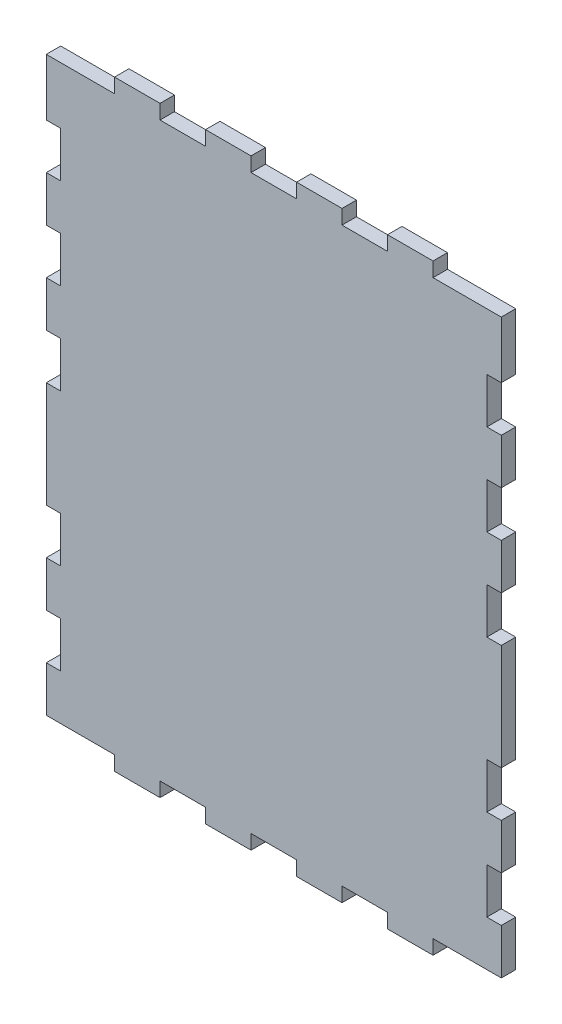
SolidWorks part; units mm, degrees
ref_plane "Front Plane" through (0, 0, 0) normal (0, 0, 1) x (1, 0, 0)
ref_plane "Top Plane" through (0, 0, 0) normal (0, 1, 0) x (1, 0, 0)
ref_plane "Right Plane" through (0, 0, 0) normal (1, 0, 0) x (0, 0, -1)
sketch "Sketch1" plane through (0, 0, -77.7349) normal (0, 0, -1) x (-1, 0, 0)
  line L37 (0, 100) -> (30, 100)
  line L38 (0, 100) -> (0, 101.5875)
  line L39 (0, 101.5875) -> (30, 101.5875)
  line L40 (30, 100) -> (30, 101.5875)
  line L41 (50, 100) -> (70, 100)
  line L42 (50, 100) -> (50, 101.5875)
  line L43 (50, 101.5875) -> (70, 101.5875)
  line L44 (70, 100) -> (70, 101.5875)
  line L45 (110, 101.5875) -> (90, 101.5875)
  line L46 (110, 101.5875) -> (110, 100)
  line L47 (110, 100) -> (90, 100)
  line L48 (90, 101.5875) -> (90, 100)
  line L49 (150, 101.5875) -> (130, 101.5875)
  line L50 (150, 101.5875) -> (150, 100)
  line L51 (150, 100) -> (130, 100)
  line L52 (130, 101.5875) -> (130, 100)
  line L53 (170, 100) -> (200, 100)
  line L54 (170, 100) -> (170, 101.5875)
  line L55 (170, 101.5875) -> (200, 101.5875)
  line L56 (200, 100) -> (200, 101.5875)
  line L268 (0, 80) -> (6.35, 80)
  line L269 (6.35, 80) -> (6.35, 60)
  line L270 (6.35, 60) -> (0, 60)
  line L271 (0, 60) -> (0, 40)
  line L272 (0, 40) -> (6.35, 40)
  line L273 (6.35, 40) -> (6.35, 20)
  line L274 (6.35, 20) -> (0, 20)
  line L275 (0, 20) -> (0, 0)
  line L276 (0, 0) -> (30, 0)
  line L277 (30, 0) -> (30, -6.35)
  line L278 (30, -6.35) -> (50, -6.35)
  line L279 (50, -6.35) -> (50, 0)
  line L280 (50, 0) -> (70, 0)
  line L281 (70, 0) -> (70, -6.35)
  line L282 (70, -6.35) -> (90, -6.35)
  line L283 (90, -6.35) -> (90, 0)
  line L284 (90, 0) -> (110, 0)
  line L285 (110, 0) -> (110, -6.35)
  line L286 (110, -6.35) -> (130, -6.35)
  line L287 (130, -6.35) -> (130, 0)
  line L288 (130, 0) -> (150, 0)
  line L289 (150, 0) -> (150, -6.35)
  line L290 (150, -6.35) -> (170, -6.35)
  line L291 (170, -6.35) -> (170, 0)
  line L292 (170, 0) -> (200, 0)
  line L293 (200, 0) -> (200, 20)
  line L294 (200, 20) -> (193.65, 20)
  line L295 (193.65, 20) -> (193.65, 40)
  line L296 (193.65, 40) -> (200, 40)
  line L297 (200, 40) -> (200, 60)
  line L298 (200, 60) -> (193.65, 60)
  line L299 (193.65, 60) -> (193.65, 80)
  line L300 (193.65, 80) -> (200, 80)
  line L301 (200, 80) -> (200, 100)
  line L302 (200, 100) -> (170, 100)
  line L303 (170, 100) -> (170, 101.5875)
  line L304 (170, 101.5875) -> (150, 101.5875)
  line L305 (150, 101.5875) -> (150, 100)
  line L306 (150, 100) -> (130, 100)
  line L307 (130, 100) -> (130, 101.5875)
  line L308 (130, 101.5875) -> (110, 101.5875)
  line L309 (110, 101.5875) -> (110, 100)
  line L310 (110, 100) -> (90, 100)
  line L311 (90, 100) -> (90, 101.5875)
  line L312 (90, 101.5875) -> (70, 101.5875)
  line L313 (70, 101.5875) -> (70, 100)
  line L314 (70, 100) -> (50, 100)
  line L315 (50, 100) -> (50, 101.5875)
  line L316 (50, 101.5875) -> (30, 101.5875)
  line L317 (30, 101.5875) -> (30, 100)
  line L318 (30, 100) -> (0, 100)
  line L319 (0, 100) -> (0, 80)
  line L320 (0, 226.5875) -> (6.35, 226.5875)
  line L321 (6.35, 226.5875) -> (6.35, 206.5875)
  line L322 (6.35, 206.5875) -> (0, 206.5875)
  line L323 (0, 206.5875) -> (0, 186.5875)
  line L324 (0, 186.5875) -> (6.35, 186.5875)
  line L325 (6.35, 186.5875) -> (6.35, 166.5875)
  line L326 (6.35, 166.5875) -> (0, 166.5875)
  line L327 (0, 166.5875) -> (0, 146.5875)
  line L328 (0, 146.5875) -> (6.35, 146.5875)
  line L329 (6.35, 146.5875) -> (6.35, 126.5875)
  line L330 (6.35, 126.5875) -> (0, 126.5875)
  line L331 (0, 126.5875) -> (0, 101.5875)
  line L332 (0, 101.5875) -> (30, 101.5875)
  line L333 (30, 101.5875) -> (30, 100)
  line L334 (30, 100) -> (50, 100)
  line L335 (50, 100) -> (50, 101.5875)
  line L336 (50, 101.5875) -> (70, 101.5875)
  line L337 (70, 101.5875) -> (70, 100)
  line L338 (70, 100) -> (90, 100)
  line L339 (90, 100) -> (90, 101.5875)
  line L340 (90, 101.5875) -> (110, 101.5875)
  line L341 (110, 101.5875) -> (110, 100)
  line L342 (110, 100) -> (130, 100)
  line L343 (130, 100) -> (130, 101.5875)
  line L344 (130, 101.5875) -> (150, 101.5875)
  line L345 (150, 101.5875) -> (150, 100)
  line L346 (150, 100) -> (170, 100)
  line L347 (170, 100) -> (170, 101.5875)
  line L348 (170, 101.5875) -> (200, 101.5875)
  line L349 (200, 101.5875) -> (200, 126.5875)
  line L350 (200, 126.5875) -> (193.65, 126.5875)
  line L351 (193.65, 126.5875) -> (193.65, 146.5875)
  line L352 (193.65, 146.5875) -> (200, 146.5875)
  line L353 (200, 146.5875) -> (200, 166.5875)
  line L354 (200, 166.5875) -> (193.65, 166.5875)
  line L355 (193.65, 166.5875) -> (193.65, 186.5875)
  line L356 (193.65, 186.5875) -> (200, 186.5875)
  line L357 (200, 186.5875) -> (200, 206.5875)
  line L358 (200, 206.5875) -> (193.65, 206.5875)
  line L359 (193.65, 206.5875) -> (193.65, 226.5875)
  line L360 (193.65, 226.5875) -> (200, 226.5875)
  line L361 (200, 226.5875) -> (200, 251.5875)
  line L362 (200, 251.5875) -> (170, 251.5875)
  line L363 (170, 251.5875) -> (170, 257.9375)
  line L364 (170, 257.9375) -> (150, 257.9375)
  line L365 (150, 257.9375) -> (150, 251.5875)
  line L366 (150, 251.5875) -> (130, 251.5875)
  line L367 (130, 251.5875) -> (130, 257.9375)
  line L368 (130, 257.9375) -> (110, 257.9375)
  line L369 (110, 257.9375) -> (110, 251.5875)
  line L370 (110, 251.5875) -> (90, 251.5875)
  line L371 (90, 251.5875) -> (90, 257.9375)
  line L372 (90, 257.9375) -> (70, 257.9375)
  line L373 (70, 257.9375) -> (70, 251.5875)
  line L374 (70, 251.5875) -> (50, 251.5875)
  line L375 (50, 251.5875) -> (50, 257.9375)
  line L376 (50, 257.9375) -> (30, 257.9375)
  line L377 (30, 257.9375) -> (30, 251.5875)
  line L378 (30, 251.5875) -> (0, 251.5875)
  line L379 (0, 251.5875) -> (0, 226.5875)
extrude "Boss-Extrude1" add sketch "Sketch1" against normal blind 6.35 contours L378 L379 L320 L321 L322 L323 L324 L325 L326 L327 L328 L329 L330 L331 L39 L316 L43 L312 L45 L308 L49 L304 L55 L349 L350 L351 L352 L353 L354 L355 L356 L357 L358 L359 L360 L361 L362 L363 L364 L365 L366 L367 L368 L369 L370 L371 L372 L373 L374 L375 L376 | L346 L51 L342 L47 L338 L41 L334 L37 L319 L268 L269 L270 L271 L272 L273 L274 L275 L276 L277 L278 L279 L280 L281 L282 L283 L284 L285 L286 L287 L288 L289 L290 L291 L292 L293 L294 L295 L296 L297 L298 L299 L300 L301 L53 | L37 L40 L39 L38 | L40 L334 L42 L316 | L41 L44 L43 L42 | L44 L338 L48 L312 | L45 L48 L47 L46 | L46 L342 L52 L308 | L49 L52 L51 L50 | L50 L346 L54 L304 | L53 L56 L55 L54
